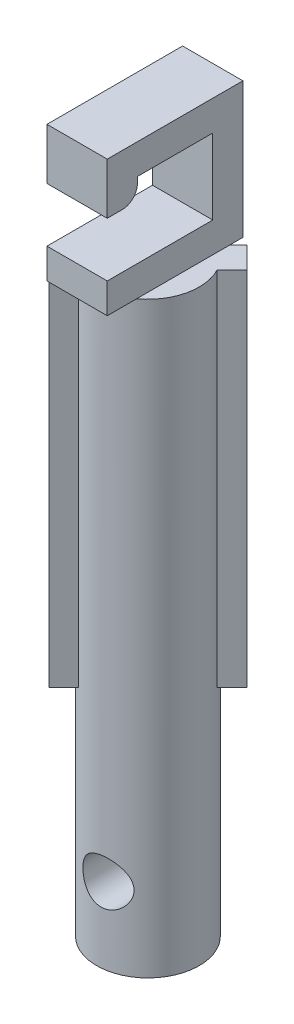
SolidWorks part; units mm, degrees
ref_plane "Front Plane" through (0, 0, 0) normal (0, 0, 1) x (1, 0, 0)
ref_plane "Top Plane" through (0, 0, 0) normal (0, 1, 0) x (1, 0, 0)
ref_plane "Right Plane" through (0, 0, 0) normal (1, 0, 0) x (0, 0, -1)
sketch "Sketch1" plane through (0, 0, 0) normal (0, 1, 0) x (1, 0, 0)
  circle A0 centre (0, 0) radius 1.7
  dimension "D1" = 3.4
extrude "main shaft" add sketch "Sketch1" along normal mid plane 12
sketch "Sketch2" plane through (0, 6, 0) normal (0, 1, 0) x (1, 0, 0)
  line L0 (3.2385, 3.2385) -> (-4.1755, -4.1755) construction
  line L1 (-0.7954, -1.5025) -> (-1.2903, -1.9974)
  line L2 (-1.2903, -1.9974) -> (-1.9974, -1.2903)
  line L3 (-1.9974, -1.2903) -> (-1.5025, -0.7954)
  line L4 (-1.9627, 1.9627) -> (2.0335, -2.0335) construction
  line L5 (1.2903, 1.9974) -> (0.7954, 1.5025)
  line L6 (1.9974, 1.2903) -> (1.2903, 1.9974)
  line L7 (1.5025, 0.7954) -> (1.9974, 1.2903)
  arc A0 (-1.5025, -0.7954) -> (-0.7954, -1.5025) centre (0, 0) ccw
  arc A1 (0.7954, 1.5025) -> (1.5025, 0.7954) centre (0, 0) cw
  circle A2 centre (0, 0) radius 1.7 construction
  point P8 (-1.0428, -1.75)
  dimension "D1" = 1
  dimension "D2" = 0.7
extrude "guides" add sketch "Sketch2" against normal blind 12
sketch "Sketch21" plane through (0, 6, 0) normal (0, 1, 0) x (1, 0, 0)
  line L0 (0, 0) -> (0, -1.7) construction
  line L1 (-1, 2.15) -> (1, 2.15)
  line L2 (-1, 2.15) -> (-1, -2.35)
  line L3 (-1, -2.35) -> (1, -2.35)
  line L4 (1, 2.15) -> (1, -2.35)
  line L5 (-1, 2.15) -> (1, -2.35) construction
  line L6 (-1, -2.35) -> (1, 2.15) construction
  arc A0 (-0.7954, -1.5025) -> (1.5025, 0.7954) centre (0, 0) ccw construction
  point P0 (0, -0.1)
  dimension "D1" = 4.5
  dimension "D2" = 2
  dimension "D3" = 0.1
extrude "hook extrude" add sketch "Sketch21" along normal blind 4.5
sketch "Sketch22" plane through (1, 0, 0) normal (1, 0, 0) x (0, 0, -1)
  line L0 (0.7954, 6) -> (-1.3748, 6) construction
  line L1 (1.15, 7) -> (44.9676, 7)
  line L2 (1.15, 7) -> (1.15, 9.5)
  line L3 (1.15, 9.5) -> (-1.35, 9.5)
  line L4 (-1.35, 8.8) -> (-1.35, 9.5)
  line L5 (1.15, 7) -> (-1.35, 9.5) construction
  line L6 (1.15, 9.5) -> (44.9676, 7) construction
  line L7 (-2.35, 10.5) -> (2.15, 10.5) construction
  line L8 (-1.35, 8.8) -> (-2.35, 8.8)
  line L9 (-2.35, 10.5) -> (-2.35, 6) construction
  line L10 (-2.35, 8.8) -> (-2.35, 7)
  line L11 (-2.35, 7) -> (44.9676, 7)
  point P0 (-1.5013, 9.6513)
  line M10 (-2.35, 10.5) -> (-2.35, 6)
  dimension "D1" = 2.5
  dimension "D2" = 1
  dimension "D3" = 1
  dimension "D4" = 1
  dimension "D5" = 0.7
extrude "hook cut" cut sketch "Sketch22" against normal through all contours L11 L2 L3 L4 L8 M10
fillet "hook fillet" radius 0.5 1 edges at (0, 8.8, 1.35)
sketch "Sketch23" plane through (0, -6, 0) normal (0, -1, 0) x (1, 0, 0)
  circle A0 centre (0, 0) radius 1.7
  dimension "D1" = 3.4
extrude "top stopper" add sketch "Sketch23" along normal blind 2
sketch "Sketch24" plane through (0, -8, 0) normal (0, -1, 0) x (1, 0, 0)
  circle A0 centre (0, 0) radius 1.7
  dimension "D1" = 3.4
extrude "bottom shaft" add sketch "Sketch24" along normal blind 5.5
ref_plane "Plane4" through (0, 0, 2.35) normal (0, 0, 1) x (1, 0, 0)
hole_wizard "Ø1.5mm Dowel Hole2" positions "Sketch27" profile "Sketch26" hole size "Ø1.5" standard "ISO" end condition through all
sketch "Sketch27" plane through (0, 0, 2.35) normal (0, 0, 1) x (1, 0, 0)
  line L0 (-1.7, -13.5) -> (1.7, -13.5) construction
  line L1 (-1.7, 6) -> (-1.7, -13.5) construction
  point P0 (0.2, -11)
  dimension "D1" = 2.5
  dimension "D2" = 1.9
sketch "Sketch26" plane through (0.2, -11, 2.35) normal (1, 0, 0) x (0, -1, 0)
  line L0 (0, 0) -> (0, 4.5)
  line L1 (0, 4.5) -> (0.75, 4.5)
  line L2 (0.75, 4.5) -> (0.75, 0)
  line L5 (0.75, 0) -> (0, 0)
  line L11 (0, -6.35) -> (0, 107.95) construction
  dimension "Thru Hole Dia." = 1.5
  dimension "Thru Hole Depth" = 4.5
